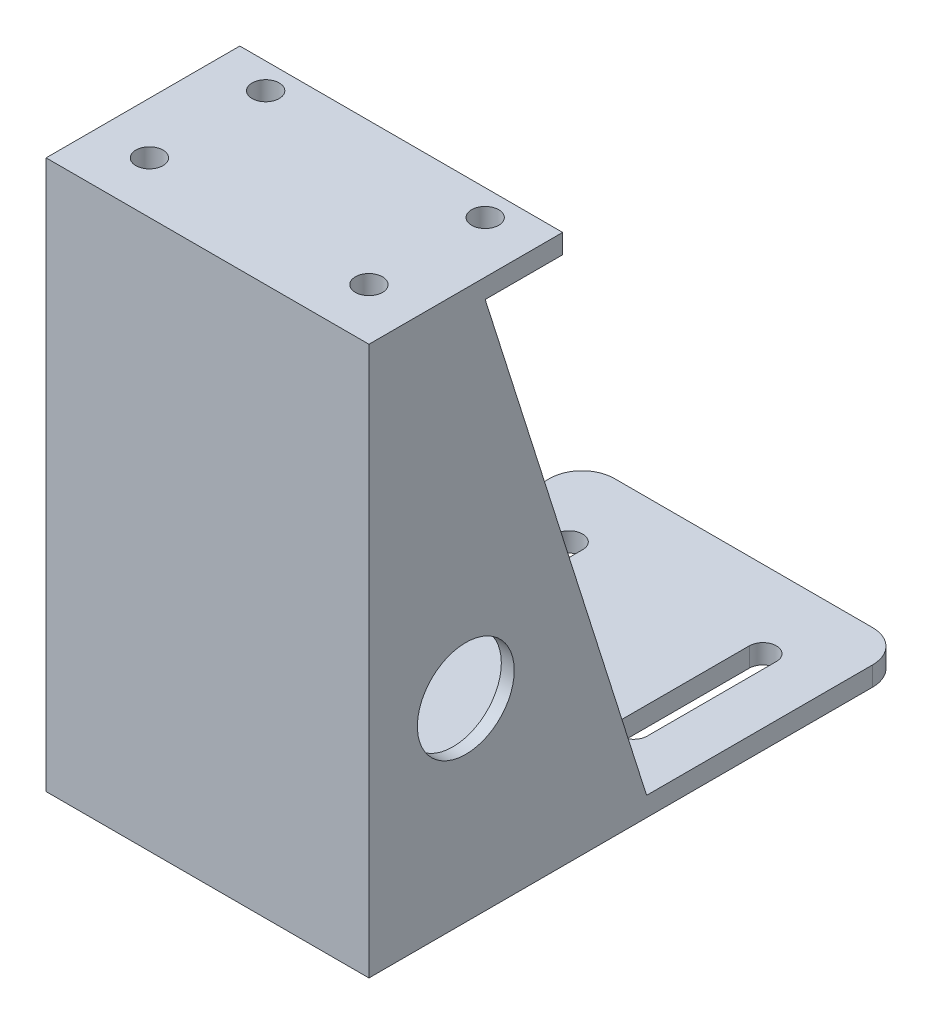
SolidWorks part; units mm, degrees
ref_plane "前视基准面" through (0, 0, 0) normal (0, 0, 1) x (1, 0, 0)
ref_plane "上视基准面" through (0, 0, 0) normal (0, 1, 0) x (1, 0, 0)
ref_plane "右视基准面" through (0, 0, 0) normal (1, 0, 0) x (0, 0, -1)
sketch "草图1" plane through (0, 0, 0) normal (1, 0, 0) x (0, 0, -1)
  line L0 (0, 0) -> (0, 85)
  line L1 (30, 85) -> (30, 82)
  line L2 (30, 82) -> (3, 82)
  line L3 (3, 82) -> (3, 3)
  line L4 (3, 3) -> (83, 3)
  line L5 (83, 3) -> (83, 0)
  line L6 (83, 0) -> (0, 0)
  line L7 (0, 85) -> (30, 85)
  dimension "D1" = 30
  dimension "D2" = 3
  dimension "D3" = 3
  dimension "D4" = 3
  dimension "D5" = 80
  dimension "D6" = 85
extrude "凸台-拉伸1" add sketch "草图1" along normal mid plane 50
sketch "草图2" plane through (25, 0, 0) normal (1, 0, 0) x (0, 0, -1)
  line L2 (83, 3) -> (3, 3) construction
  line L3 (43, 3) -> (3, 3)
  line L5 (18, 82) -> (3, 82)
  line L6 (3, 82) -> (30, 82) construction
  line L9 (18, 82) -> (43, 3)
  line L10 (3, 3) -> (3, 82)
  dimension "D1" = 15
  dimension "D3" = 40
sketch "草图4" plane through (0, 85, 0) normal (0, 1, 0) x (1, 0, 0)
  line L0 (0, 0) -> (0, 30) construction
  line L1 (25, 30) -> (-25, 30) construction
  line L2 (-25, 30) -> (-25, 0) construction
  line L3 (25, 0) -> (-25, 0) construction
  circle A0 centre (-17, 26) radius 2.1
  circle A1 centre (-17, 8) radius 2.1
  circle A2 centre (17, 8) radius 2.1
  circle A3 centre (17, 26) radius 2.1
  dimension "D1" = 4.2
  dimension "D2" = 4.2
  dimension "D3" = 8
  dimension "D4" = 8
  dimension "D5" = 18
  dimension "D6" = 8
extrude "凸台-拉伸2" add sketch "草图2" against normal blind 2
extrude "切除-拉伸1" cut sketch "草图4" against normal up to next
sketch "草图5" plane through (0, 0, 0) normal (0, -1, 0) x (1, 0, 0)
  line L0 (0, 0) -> (0, -86.1083) construction
  line L1 (-15, -11) -> (-15, -31) construction
  line L2 (-12.9, -11) -> (-12.9, -31)
  line L3 (-17.1, -11) -> (-17.1, -31)
  line L4 (-15, -51) -> (-15, -71) construction
  line L5 (-12.9, -51) -> (-12.9, -71)
  line L6 (-17.1, -51) -> (-17.1, -71)
  line L7 (15, -51) -> (15, -71) construction
  line L8 (12.9, -51) -> (12.9, -71)
  line L9 (17.1, -51) -> (17.1, -71)
  line L10 (15, -11) -> (15, -31) construction
  line L11 (12.9, -11) -> (12.9, -31)
  line L12 (17.1, -11) -> (17.1, -31)
  line L13 (25, -83) -> (-25, -83) construction
  arc A0 (-12.9, -11) -> (-17.1, -11) centre (-15, -11) ccw
  arc A1 (-17.1, -31) -> (-12.9, -31) centre (-15, -31) ccw
  arc A2 (-12.9, -51) -> (-17.1, -51) centre (-15, -51) ccw
  arc A3 (-17.1, -71) -> (-12.9, -71) centre (-15, -71) ccw
  arc A4 (12.9, -51) -> (17.1, -51) centre (15, -51) cw
  arc A5 (17.1, -71) -> (12.9, -71) centre (15, -71) cw
  arc A6 (12.9, -11) -> (17.1, -11) centre (15, -11) cw
  arc A7 (17.1, -31) -> (12.9, -31) centre (15, -31) cw
  point P5 (-15, -21)
  point P10 (-15, -61)
  point P20 (15, -61)
  point P27 (15, -21)
  dimension "D1" = 2.1
  dimension "D2" = 2.1
  dimension "D3" = 20
  dimension "D4" = 20
  dimension "D5" = 40
  dimension "D6" = 22
  dimension "D7" = 30
extrude "切除-拉伸2" cut sketch "草图5" against normal up to next
fillet "圆角1" radius 5 2 edges at (-25, 1.5, -83) (25, 1.5, -83)
sketch "草图6" plane through (-25, 0, 0) normal (-1, 0, 0) x (0, 0, 1)
  line L4 (-43, 3) -> (-3, 3)
  line L5 (-3, 3) -> (-3, 82)
  line L6 (-3, 82) -> (-18, 82)
  line L7 (-18, 82) -> (-43, 3)
  line L8 (-43, 3) -> (-3, 3)
  line L9 (-3, 3) -> (-3, 82)
  line L10 (-3, 82) -> (-18, 82)
  line L11 (-18, 82) -> (-43, 3)
  dimension "D1" = 0
extrude "凸台-拉伸3" add sketch "草图6" against normal blind 2
sketch "草图7" plane through (25, 0, 0) normal (1, 0, 0) x (0, 0, -1)
  line L0 (0, 0) -> (78, 0) construction
  line L1 (0, 85) -> (0, 0) construction
  circle A0 centre (15, 30) radius 7.5
  dimension "D1" = 15
  dimension "D2" = 30
  dimension "D3" = 15
extrude "切除-拉伸3" cut sketch "草图7" against normal through all
